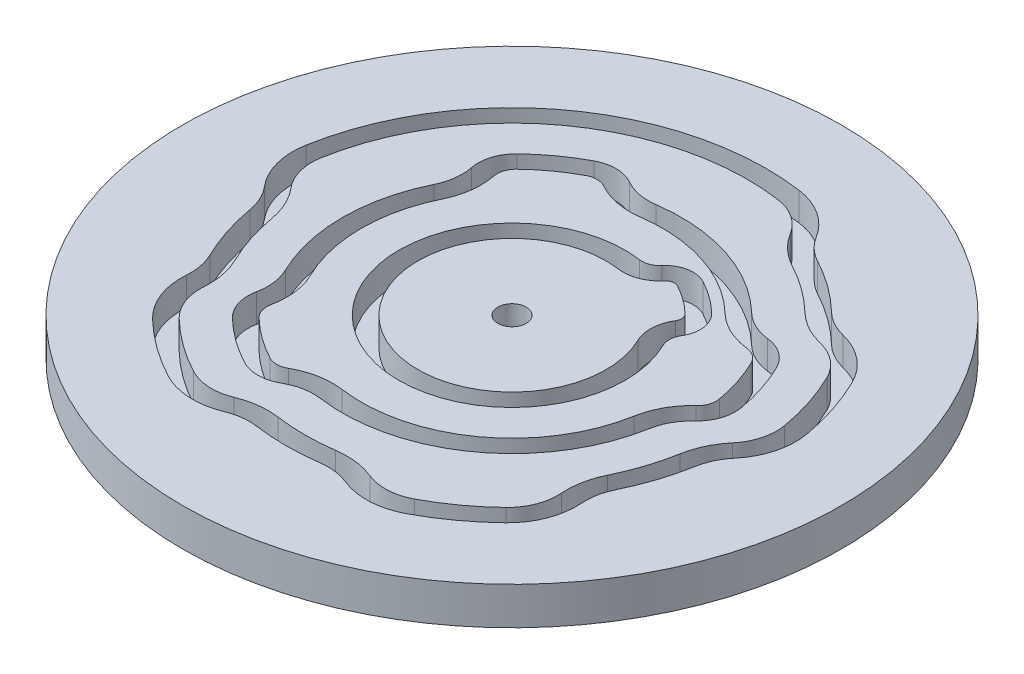
SolidWorks part; units mm, degrees
ref_plane "前视基准面" through (0, 0, 0) normal (0, 0, 1) x (1, 0, 0)
ref_plane "上视基准面" through (0, 0, 0) normal (0, 1, 0) x (1, 0, 0)
ref_plane "右视基准面" through (0, 0, 0) normal (1, 0, 0) x (0, 0, -1)
sketch "草图1" plane through (0, 0, 0) normal (0, 1, 0) x (1, 0, 0)
  line L0 (0, 0) -> (35, 0) construction
  line L1 (0, 0) -> (28.3156, -20.5725) construction
  line L2 (0, 0) -> (10.8156, -33.287) construction
  line L3 (0, 0) -> (-10.8156, -33.287) construction
  line L4 (0, 0) -> (-28.3156, -20.5725) construction
  line L5 (0, 0) -> (-35, 0) construction
  line L6 (0, 0) -> (-28.3156, 20.5725) construction
  line L7 (0, 0) -> (-10.8156, 33.287) construction
  line L8 (0, 0) -> (10.8156, 33.287) construction
  line L9 (0, 0) -> (28.3156, 20.5725) construction
  line L10 (0, 0) -> (24.313, 25.1769) construction
  line L11 (0, 0) -> (31.4578, 15.343) construction
  line L12 (0, 0) -> (34.4683, 6.0777) construction
  line L13 (0, 0) -> (34.4683, -6.0777) construction
  line L14 (0, 0) -> (31.4578, -15.343) construction
  line L15 (0, 0) -> (24.313, -25.1769) construction
  line L16 (0, 0) -> (16.4315, -30.9032) construction
  line L17 (0, 0) -> (4.8711, -34.6594) construction
  line L18 (0, 0) -> (-4.8711, -34.6594) construction
  line L19 (0, 0) -> (-16.4315, -30.9032) construction
  line L20 (0, 0) -> (-24.313, -25.1769) construction
  line L21 (0, 0) -> (-31.4578, -15.343) construction
  line L22 (0, 0) -> (-34.4683, -6.0777) construction
  line L23 (0, 0) -> (-34.4683, 6.0777) construction
  line L24 (0, 0) -> (-31.4578, 15.343) construction
  line L25 (0, 0) -> (-24.313, 25.1769) construction
  line L26 (0, 0) -> (-16.4315, 30.9032) construction
  line L27 (0, 0) -> (-4.8711, 34.6594) construction
  line L28 (0, 0) -> (4.8711, 34.6594) construction
  line L29 (0, 0) -> (16.4315, 30.9032) construction
  circle A0 centre (0, 0) radius 35 construction
  circle A1 centre (0, 0) radius 10 construction
  circle A2 centre (0, 0) radius 12 construction
  circle A3 centre (0, 0) radius 13 construction
  circle A4 centre (0, 0) radius 15 construction
  circle A5 centre (0, 0) radius 16 construction
  circle A6 centre (0, 0) radius 18 construction
  circle A7 centre (0, 0) radius 19 construction
  circle A8 centre (0, 0) radius 21 construction
  circle A9 centre (0, 0) radius 22 construction
  circle A10 centre (0, 0) radius 24 construction
  circle A11 centre (0, 0) radius 25 construction
  circle A12 centre (0, 0) radius 27 construction
  circle A13 centre (0, 0) radius 28 construction
  circle A14 centre (0, 0) radius 30 construction
  circle A15 centre (0, 0) radius 31 construction
  circle A16 centre (0, 0) radius 33 construction
  point P17 (0, 0)
  point P38 (0, 0)
  dimension "D1" = 70
  dimension "D2" = 20
  dimension "D7" = 2
  dimension "D8" = 1
  dimension "D9" = 2
  dimension "D10" = 1
  dimension "D11" = 2
  dimension "D12" = 1
  dimension "D13" = 2
  dimension "D14" = 1
  dimension "D15" = 2
  dimension "D16" = 1
  dimension "D17" = 2
  dimension "D18" = 1
  dimension "D19" = 2
  dimension "D20" = 1
  dimension "D21" = 2
  dimension "D4" = 10
  dimension "D5" = 10
  dimension "D3" = 10
  dimension "D6" = 10
sketch "草图2" plane through (0, 0, 0) normal (0, 1, 0) x (1, 0, 0)
  line L0 (-161803.3989, -117557.0505) -> (161831.7145, 117577.6229) construction
  line L1 (-200000, 0) -> (200035, 0) construction
  line L2 (0, 0) -> (-4.8711, 34.6594) construction
  line L3 (0, 0) -> (-10.8156, -33.287) construction
  line L4 (0, 0) -> (-16.4315, -30.9032) construction
  line L5 (0, 0) -> (-4.8711, -34.6594) construction
  line L6 (0, 0) -> (-34.4683, -6.0777) construction
  line L7 (0, 0) -> (31.4578, 15.343) construction
  line L8 (0, 0) -> (24.313, 25.1769) construction
  line L9 (0, 0) -> (-34.4683, 6.0777) construction
  line L10 (0, 0) -> (-31.4578, -15.343) construction
  line L11 (0, 0) -> (4.8711, 34.6594) construction
  line L12 (0, 0) -> (16.4315, 30.9032) construction
  line L13 (0, 0) -> (-24.313, -25.1769) construction
  line L14 (0, 0) -> (34.4683, -6.0777) construction
  line L15 (0, 0) -> (34.4683, 6.0777) construction
  line L16 (0, 0) -> (-24.313, 25.1769) construction
  line L18 (0, 0) -> (4.8711, -34.6594) construction
  line L19 (0, 0) -> (16.4315, -30.9032) construction
  line L20 (0, 0) -> (24.313, -25.1769) construction
  line L21 (0, 0) -> (31.4578, -15.343) construction
  arc A0 (8.9879, 4.3837) -> (9.1782, 8.1695) centre (12.5152, 6.1041) cw
  arc A1 (17.0771, 8.3291) -> (15.5035, 9.4406) centre (15.2778, 7.4515) ccw
  circle A2 centre (0, 0) radius 10 construction
  arc A3 (15.5035, 9.4406) -> (11.1145, 11.5094) centre (16.3542, 16.9352) cw
  arc A4 (9.1782, 8.1695) -> (9.0306, 9.3514) centre (8.3714, 8.6689) ccw
  arc A5 (12.5039, 12.9481) -> (15.7291, 11.4279) centre (16.3542, 16.9352) ccw
  circle A6 centre (0, 0) radius 13 construction
  arc A7 (15.7291, 11.4279) -> (18.8747, 9.2058) centre (15.2778, 7.4515) cw
  arc A8 (10.7855, 5.2605) -> (10.8788, 7.1169) centre (12.5152, 6.1041) cw
  arc A9 (17.0771, 8.3291) -> (18.7113, 3.2993) centre (0, 0) cw
  circle A10 centre (0, 0) radius 12 construction
  arc A11 (18.8747, 9.2058) -> (20.681, 3.6466) centre (0, 0) cw
  arc A12 (10.8788, 7.1169) -> (10.4199, 10.7901) centre (8.3714, 8.6689) ccw
  circle A13 centre (0, 0) radius 15 construction
  arc A14 (6.1031, 11.4783) -> (4.9334, 11.2535) centre (5.6577, 10.6405) ccw
  arc A15 (4.9334, 11.2535) -> (1.3917, 9.9027) centre (1.9379, 13.789) cw
  arc A16 (7.0421, 13.2442) -> (3.4069, 12.5457) centre (5.6577, 10.6405) ccw
  arc A17 (3.4069, 12.5457) -> (1.6701, 11.8832) centre (1.9379, 13.789) cw
  arc A18 (7.0421, 13.2442) -> (10.4199, 10.7901) centre (0, 0) cw
  arc A19 (6.1031, 11.4783) -> (9.0306, 9.3514) centre (0, 0) cw
  arc A20 (10.7855, 5.2605) -> (1.6701, 11.8832) centre (0, 0) cw
  arc A21 (1.3917, 9.9027) -> (8.9879, 4.3837) centre (0, 0) ccw
  arc A22 (15.7569, -2.7784) -> (18.0917, 1.4751) centre (23.1851, -4.0882) cw
  arc A23 (12.5039, 12.9481) -> (-2.5051, 17.8248) centre (0, 0) ccw
  circle A24 centre (0, 0) radius 16 construction
  arc A25 (11.1145, 11.5094) -> (-2.2268, 15.8443) centre (0, 0) ccw
  arc A26 (18.0917, 1.4751) -> (18.7113, 3.2993) centre (16.7399, 2.9517) ccw
  circle A27 centre (0, 0) radius 19 construction
  arc A28 (17.7265, -3.1257) -> (19.4422, 0) centre (23.1851, -4.0882) cw
  arc A29 (-13.1985, 13.6675) -> (-13.7694, 11.8274) centre (-11.8079, 12.2274) ccw
  circle A30 centre (0, 0) radius 18 construction
  arc A31 (-14.5878, 15.1061) -> (-9.8589, 18.5419) centre (0, 0) cw
  arc A32 (19.4422, 0) -> (20.681, 3.6466) centre (16.7399, 2.9517) ccw
  arc A33 (-13.1985, 13.6675) -> (-8.92, 16.776) centre (0, 0) cw
  circle A34 centre (0, 0) radius 21 construction
  arc A35 (-15.7291, 11.4279) -> (-14.5878, 15.1061) centre (-11.8079, 12.2274) cw
  arc A36 (-16.1783, 7.8907) -> (-15.7291, 11.4279) centre (-21.1601, 10.3205) ccw
  arc A37 (-13.7694, 11.8274) -> (-14.3807, 7.0139) centre (-21.1601, 10.3205) cw
  arc A38 (-6.9936, 16.7504) -> (-8.92, 16.776) centre (-7.9801, 15.0084) ccw
  arc A39 (-6.008, 18.4907) -> (-9.8589, 18.5419) centre (-7.9801, 15.0084) ccw
  arc A40 (-2.5051, 17.8248) -> (-6.008, 18.4907) centre (-3.2765, 23.3136) cw
  arc A41 (-2.2268, 15.8443) -> (-6.9936, 16.7504) centre (-3.2765, 23.3136) cw
  arc A42 (-14.3807, 7.0139) -> (-14.3807, -7.0139) centre (0, 0) ccw
  arc A43 (-16.1783, 7.8907) -> (-16.1783, -7.8907) centre (0, 0) ccw
  arc A44 (-8.92, -16.776) -> (-6.9936, -16.7504) centre (-7.9801, -15.0084) ccw
  arc A45 (-9.8589, -18.5419) -> (-14.5878, -15.1061) centre (0, 0) cw
  arc A46 (-8.92, -16.776) -> (-13.1985, -13.6675) centre (0, 0) cw
  arc A47 (-6.008, -18.4907) -> (-9.8589, -18.5419) centre (-7.9801, -15.0084) cw
  arc A48 (-2.5051, -17.8248) -> (-6.008, -18.4907) centre (-3.2765, -23.3136) ccw
  arc A49 (-6.9936, -16.7504) -> (-2.2268, -15.8443) centre (-3.2765, -23.3136) cw
  arc A50 (-13.7694, -11.8274) -> (-13.1985, -13.6675) centre (-11.8079, -12.2274) ccw
  arc A51 (-15.7291, -11.4279) -> (-14.5878, -15.1061) centre (-11.8079, -12.2274) ccw
  arc A52 (-16.1783, -7.8907) -> (-15.7291, -11.4279) centre (-21.1601, -10.3205) cw
  arc A53 (-14.3807, -7.0139) -> (-13.7694, -11.8274) centre (-21.1601, -10.3205) cw
  arc A54 (-2.2268, -15.8443) -> (11.1145, -11.5094) centre (0, 0) ccw
  arc A55 (-2.5051, -17.8248) -> (12.5039, -12.9481) centre (0, 0) ccw
  arc A56 (12.5039, -12.9481) -> (17.7265, -3.1257) centre (0, 0) ccw
  arc A57 (11.1145, -11.5094) -> (15.7569, -2.7784) centre (0, 0) ccw
  arc A58 (21.6658, -3.8203) -> (23.4373, -0.0399) centre (29.5525, -5.2109) cw
  circle A59 centre (0, 0) radius 22 construction
  arc A60 (23.4373, -0.0399) -> (24.6202, 4.3412) centre (19.3543, 3.4127) ccw
  circle A61 centre (0, 0) radius 25 construction
  arc A62 (23.6354, -4.1676) -> (24.9645, -1.3313) centre (29.5525, -5.2109) cw
  arc A63 (16.6718, 17.2642) -> (19.4142, 15.7508) centre (20.8456, 21.5862) ccw
  circle A64 centre (0, 0) radius 24 construction
  arc A65 (19.4142, 15.7508) -> (24.2674, 11.836) centre (17.6639, 8.6153) cw
  arc A66 (15.2825, 15.8255) -> (18.9378, 13.8084) centre (20.8456, 21.5862) ccw
  arc A67 (18.9378, 13.8084) -> (22.4699, 10.9593) centre (17.6639, 8.6153) cw
  arc A68 (11.2673, 21.1907) -> (8.9806, 23.3313) centre (14.0881, 26.4958) cw
  arc A69 (24.9645, -1.3313) -> (26.5898, 4.6885) centre (19.3543, 3.4127) ccw
  circle A70 centre (0, 0) radius 27 construction
  arc A71 (8.9806, 23.3313) -> (3.7577, 26.7372) centre (2.7352, 19.4617) ccw
  arc A72 (7.2805, 22.2779) -> (10.3284, 19.4248) centre (14.0881, 26.4958) ccw
  arc A73 (7.2805, 22.2779) -> (3.4793, 24.7567) centre (2.7352, 19.4617) ccw
  arc A74 (-23.6354, -4.1676) -> (-24.9645, -1.3313) centre (-29.5525, -5.2109) ccw
  arc A75 (-24.9645, -1.3313) -> (-26.5898, 4.6885) centre (-19.3543, 3.4127) cw
  arc A76 (-21.6658, -3.8203) -> (-23.4373, -0.0399) centre (-29.5525, -5.2109) ccw
  arc A77 (-23.4373, -0.0399) -> (-24.6202, 4.3412) centre (-19.3543, 3.4127) cw
  arc A78 (-21.5711, -10.5209) -> (-20.9792, -13.5967) centre (-26.9714, -13.1548) cw
  arc A79 (-20.9792, -13.5967) -> (-18.7558, -19.4222) centre (-13.6521, -14.1371) ccw
  arc A80 (-19.7735, -9.6442) -> (-18.9847, -13.7438) centre (-26.9714, -13.1548) cw
  arc A81 (-18.9847, -13.7438) -> (-17.3665, -17.9835) centre (-13.6521, -14.1371) ccw
  arc A82 (-3.3402, -23.7664) -> (-6.4483, -24.1541) centre (-4.1764, -29.7163) ccw
  arc A83 (-6.4483, -24.1541) -> (-12.6757, -23.8396) centre (-9.2265, -17.3525) cw
  arc A84 (-11.7368, -22.0737) -> (-7.2046, -22.3026) centre (-9.2265, -17.3525) ccw
  arc A85 (-7.2046, -22.3026) -> (-3.0618, -21.7859) centre (-4.1764, -29.7163) cw
  arc A86 (3.3402, -23.7664) -> (6.4483, -24.1541) centre (4.1764, -29.7163) cw
  arc A87 (6.4483, -24.1541) -> (12.6757, -23.8396) centre (9.2265, -17.3525) ccw
  arc A88 (3.0618, -21.7859) -> (7.2046, -22.3026) centre (4.1764, -29.7163) cw
  arc A89 (7.2046, -22.3026) -> (11.7368, -22.0737) centre (9.2265, -17.3525) ccw
  arc A90 (17.3665, -17.9835) -> (18.9847, -13.7438) centre (13.6521, -14.1371) ccw
  arc A91 (18.9847, -13.7438) -> (19.7735, -9.6442) centre (26.9714, -13.1548) cw
  arc A92 (18.7558, -19.4222) -> (20.9792, -13.5967) centre (13.6521, -14.1371) ccw
  arc A93 (20.9792, -13.5967) -> (21.5711, -10.5209) centre (26.9714, -13.1548) cw
  arc A94 (3.4793, 24.7567) -> (-24.6202, 4.3412) centre (0, 0) ccw
  arc A95 (-26.5898, 4.6885) -> (3.7577, 26.7372) centre (0, 0) cw
  arc A96 (11.2673, 21.1907) -> (16.6718, 17.2642) centre (0, 0) cw
  arc A97 (10.3284, 19.4248) -> (15.2825, 15.8255) centre (0, 0) cw
  arc A98 (24.2674, 11.836) -> (26.5898, 4.6885) centre (0, 0) cw
  arc A99 (23.6354, -4.1676) -> (21.5711, -10.5209) centre (0, 0) cw
  arc A100 (21.6658, -3.8203) -> (19.7735, -9.6442) centre (0, 0) cw
  arc A101 (17.3665, -17.9835) -> (11.7368, -22.0737) centre (0, 0) cw
  arc A102 (12.6757, -23.8396) -> (18.7558, -19.4222) centre (0, 0) ccw
  arc A103 (3.3402, -23.7664) -> (-3.3402, -23.7664) centre (0, 0) cw
  arc A104 (-3.0618, -21.7859) -> (3.0618, -21.7859) centre (0, 0) ccw
  arc A105 (-11.7368, -22.0737) -> (-17.3665, -17.9835) centre (0, 0) cw
  arc A106 (-12.6757, -23.8396) -> (-18.7558, -19.4222) centre (0, 0) cw
  arc A107 (-19.7735, -9.6442) -> (-21.6658, -3.8203) centre (0, 0) cw
  arc A108 (-21.5711, -10.5209) -> (-23.6354, -4.1676) centre (0, 0) cw
  arc A109 (22.4699, 10.9593) -> (24.6202, 4.3412) centre (0, 0) cw
  circle A110 centre (0, 0) radius 35
  point P49 (0, 0)
  point P60 (0, 0)
  point P101 (0, 0)
extrude "凸台-拉伸1" add sketch "草图2" along normal blind 3 contours A15 A21 A0 A4 A19 A14 | A54 A57 A22 A26 A9 A1 A3 A25 A41 A38 A33 A29 A37 A42 A53 A50 A46 A44 A49 A8 A20 A17 A16 A18 A12 | A109 A67 A66 A97 A72 A73 A94 A77 A76 A107 A80 A81 A105 A84 A85 A104 A88 A89 A101 A90 A91 A100 A58 A60 A56 A55 A48 A47 A45 A51 A52 A43 A36 A35 A31 A39 A40 A23 A5 A7 A11 A32 A28 | A110 A78 A108 A74 A75 A95 A71 A68 A96 A63 A65 A98 A69 A62 A99 A93 A92 A102 A87 A86 A103 A82 A83 A106 A79
sketch "草图3" plane through (0, 0, 0) normal (0, -1, 0) x (1, 0, 0)
  circle A0 centre (0, 0) radius 35
extrude "凸台-拉伸2" add sketch "草图3" along normal blind 1
sketch "草图4" plane through (0, 3, 0) normal (0, 1, 0) x (1, 0, 0)
  circle A0 centre (0, 0) radius 1.505
  dimension "D1" = 3.01
extrude "切除-拉伸1" cut sketch "草图4" against normal through all
